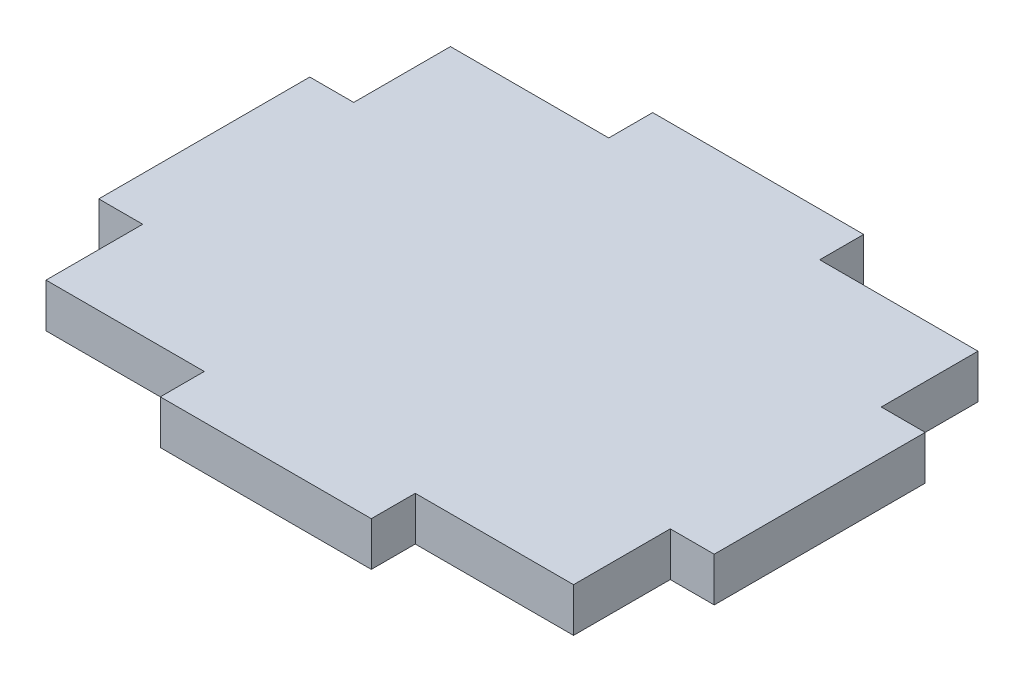
SolidWorks part; units mm, degrees
ref_plane "Front Plane" through (0, 0, 0) normal (0, 0, 1) x (1, 0, 0)
ref_plane "Top Plane" through (0, 0, 0) normal (0, 1, 0) x (1, 0, 0)
ref_plane "Right Plane" through (0, 0, 0) normal (1, 0, 0) x (0, 0, -1)
sketch "Sketch1" plane through (0, 0, 0) normal (0, 1, 0) x (1, 0, 0)
  line L1 (0, 0) -> (-76.2, 0)
  line L2 (0, 0) -> (0, -58.42)
  line L3 (0, -58.42) -> (-76.2, -58.42)
  line L4 (-76.2, 0) -> (-76.2, -58.42)
  point P24 (-87.26, 20.0636)
  dimension "D1" = 76.2
  dimension "D2" = 58.42
extrude "Boss-Extrude1" add sketch "Sketch1" along normal blind 6.35
sketch "Sketch2" plane through (0, 6.35, 0) normal (0, 1, 0) x (1, 0, 0)
  line L0 (-76.2, -58.42) -> (0, -58.42) construction
  line L1 (-22.86, -58.42) -> (-53.34, -58.42)
  line L2 (-22.86, -58.42) -> (-22.86, -64.77)
  line L3 (-22.86, -64.77) -> (-53.34, -64.77)
  line L4 (-53.34, -58.42) -> (-53.34, -64.77)
  line L5 (-76.2, 0) -> (-76.2, -58.42) construction
  line L6 (-76.2, -44.45) -> (-82.55, -44.45)
  line L7 (-76.2, -44.45) -> (-76.2, -13.97)
  line L8 (-76.2, -13.97) -> (-82.55, -13.97)
  line L9 (-82.55, -44.45) -> (-82.55, -13.97)
  line L10 (0, 0) -> (-76.2, 0) construction
  line L11 (-53.34, 0) -> (-22.86, 0)
  line L12 (-53.34, 0) -> (-53.34, 6.35)
  line L13 (-53.34, 6.35) -> (-22.86, 6.35)
  line L14 (-22.86, 0) -> (-22.86, 6.35)
  line L15 (0, -58.42) -> (0, 0) construction
  line L16 (0, -44.45) -> (6.35, -44.45)
  line L17 (0, -44.45) -> (0, -13.97)
  line L18 (0, -13.97) -> (6.35, -13.97)
  line L19 (6.35, -44.45) -> (6.35, -13.97)
  point P24 (-38.1, 0)
  point P25 (-38.1, 0)
  point P26 (-38.1, -58.42)
  point P27 (-38.1, -58.42)
  point P28 (-76.2, -29.21)
  point P29 (-76.2, -29.21)
  point P30 (0, -29.21)
  point P31 (0, -29.21)
  dimension "D1" = 30.48
  dimension "D2" = 6.35
  dimension "D3" = 0
  dimension "D4" = 30.48
  dimension "D5" = 6.35
  dimension "D6" = 0
  dimension "D7" = 30.48
  dimension "D8" = 6.35
  dimension "D9" = 0
  dimension "D10" = 0
  dimension "D11" = 6.35
  dimension "D12" = 30.48
extrude "Boss-Extrude2" add sketch "Sketch2" against normal blind 6.35
